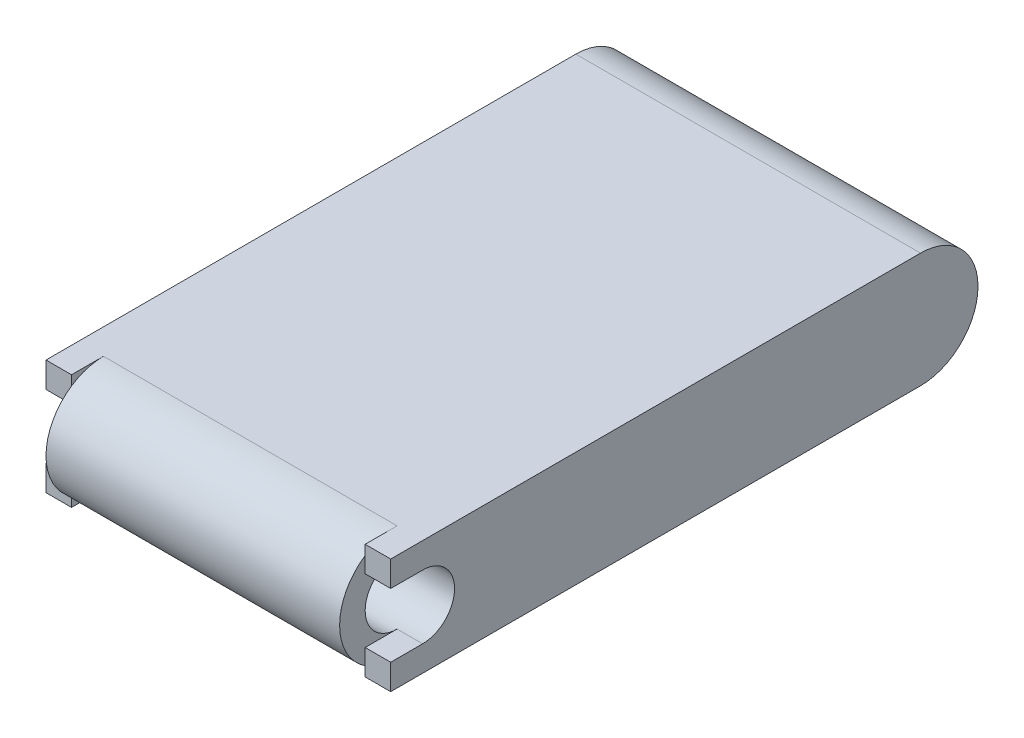
SolidWorks part; units mm, degrees
material "AISI 1035 Steel (SS)"
ref_plane "Front Plane" through (0, 0, 0) normal (0, 0, 1) x (1, 0, 0)
ref_plane "Top Plane" through (0, 0, 0) normal (0, 1, 0) x (1, 0, 0)
ref_plane "Right Plane" through (0, 0, 0) normal (1, 0, 0) x (0, 0, -1)
sketch "Sketch1" plane through (0, 0, 0) normal (1, 0, 0) x (0, 0, -1)
  line L0 (-15.7277, 3.6297) -> (15.7277, 3.6297)
  line L1 (-15.7277, -3.6297) -> (15.7277, -3.6297)
  arc A0 (-15.7277, 3.6297) -> (-15.7277, -3.6297) centre (-15.7277, 0) ccw
  arc A1 (15.7277, -3.6297) -> (15.7277, 3.6297) centre (15.7277, 0) ccw
  circle A2 centre (-15.7277, 0) radius 2.0168
  dimension "D1" = 31.4554
  dimension "D2" = 7.2593
  dimension "D3" = 7.2593
  dimension "D4" = 4.0335
extrude "Boss-Extrude2" add sketch "Sketch1" along normal blind 10.8877 and the other way blind 10.8877
sketch "Sketch2" plane through (10.8877, 0, 0) normal (1, 0, 0) x (0, 0, -1)
  circle A0 centre (-15.7277, 0) radius 3.6297
extrude "Cut-Extrude1" cut sketch "Sketch2" against normal blind 1.6129
mirror "Mirror1" about plane through (0, 0, 0) normal (1, 0, 0) of "Cut-Extrude1"
sketch "Sketch3" plane through (10.8877, 0, 0) normal (1, 0, 0) x (0, 0, -1)
  line L0 (-17.7444, -2.0168) -> (-17.7444, -3.6297)
  line L1 (-15.7277, -2.0168) -> (-17.7444, -2.0168)
  line L2 (-17.7444, 3.6297) -> (-17.7444, 2.0168)
  line L3 (-15.7277, 3.6297) -> (-17.7444, 3.6297)
  line L5 (-15.7277, -3.6297) -> (-17.7444, -3.6297)
  line L6 (-15.7277, 2.0168) -> (-17.7444, 2.0168)
  line L7 (-15.7277, 2.0168) -> (-16.1315, 2.0168) construction
  line L8 (-15.7277, -2.0168) -> (-16.1315, -2.0168) construction
  line L9 (-16.1315, 2.0168) -> (-16.1315, -2.0168) construction
  line L11 (-17.7444, 3.6297) -> (-17.7444, -3.6297) construction
  arc A1 (-15.7277, -3.6297) -> (-15.7277, 3.6297) centre (-15.7277, 0) ccw
  arc A2 (-15.7277, -2.0168) -> (-15.7277, 2.0168) centre (-15.7277, 0) ccw
  dimension "D1" = 1.6129
extrude "Boss-Extrude3" add sketch "Sketch3" against normal blind 1.6129
mirror "Mirror2" about plane through (0, 0, 0) normal (1, 0, 0) of "Boss-Extrude3"
